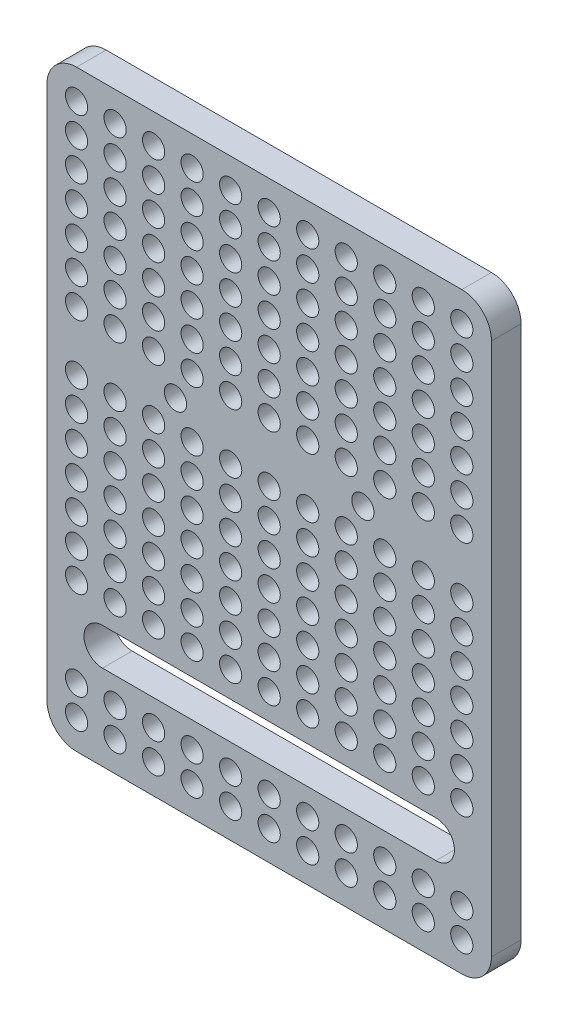
SolidWorks part; units mm, degrees
ref_plane "Спереди" through (0, 0, 0) normal (0, 0, 1) x (1, 0, 0)
ref_plane "Сверху" through (0, 0, 0) normal (0, 1, 0) x (1, 0, 0)
ref_plane "Справа" through (0, 0, 0) normal (1, 0, 0) x (0, 0, -1)
sketch "Эскиз1" plane through (0, 0, 0) normal (0, 0, 1) x (1, 0, 0)
  line L1 (4, 0) -> (56, 0)
  line L2 (0, 4) -> (0, 76)
  line L3 (4, 80) -> (56, 80)
  line L4 (60, 4) -> (60, 76)
  arc A0 (4, 0) -> (0, 4) centre (4, 4) cw
  arc A1 (56, 0) -> (60, 4) centre (56, 4) ccw
  arc A2 (56, 80) -> (60, 76) centre (56, 76) cw
  arc A3 (0, 76) -> (4, 80) centre (4, 76) cw
  point P7 (0, 0)
  point P12 (60, 80)
  point P15 (0, 80)
  dimension "D3" = 4
  dimension "D1" = 80
  dimension "D2" = 60
extrude "Бобышка-Вытянуть1" add sketch "Эскиз1" along normal blind 4 contours L3 A2 L4 A1 L1 A0 L2 A3
sketch "Эскиз2" plane through (0, 0, 4) normal (0, 0, 1) x (1, 0, 0)
  line L0 (30, 80) -> (30, 0) construction
  line L1 (4, 80) -> (56, 80) construction
  line L2 (4, 0) -> (56, 0) construction
  line L3 (7.5, 14) -> (52.5, 14) construction
  line L4 (7.5, 16.5) -> (52.5, 16.5)
  line L5 (7.5, 11.5) -> (52.5, 11.5)
  line L6 (0, 4) -> (0, 76) construction
  arc A0 (7.5, 16.5) -> (7.5, 11.5) centre (7.5, 14) ccw
  arc A1 (52.5, 11.5) -> (52.5, 16.5) centre (52.5, 14) ccw
  point P8 (30, 14)
  dimension "D1" = 11.5
  dimension "D2" = 7.5
extrude "Вырез-Вытянуть1" cut sketch "Эскиз2" against normal blind 4
sketch "Эскиз3" plane through (0, 0, 4) normal (0, 0, 1) x (1, 0, 0)
  line L0 (4, 80) -> (56, 80) construction
  line L1 (0, 4) -> (0, 76) construction
  line L2 (58.1, 64) -> (58.1, 60) construction
  line L4 (60, 4) -> (60, 76) construction
  circle A0 centre (4, 76) radius 1.5
  circle A1 centre (9.2, 76) radius 1.5
  circle A2 centre (14.4, 76) radius 1.5
  circle A3 centre (19.6, 76) radius 1.5
  circle A4 centre (24.8, 76) radius 1.5
  circle A5 centre (30, 76) radius 1.5
  circle A6 centre (35.2, 76) radius 1.5
  circle A7 centre (40.4, 76) radius 1.5
  circle A8 centre (45.6, 76) radius 1.5
  circle A9 centre (50.8, 76) radius 1.5
  circle A10 centre (56, 76) radius 1.5
  circle A11 centre (4, 72) radius 1.5
  circle A12 centre (9.2, 72) radius 1.5
  circle A13 centre (14.4, 72) radius 1.5
  circle A14 centre (19.6, 72) radius 1.5
  circle A15 centre (24.8, 72) radius 1.5
  circle A16 centre (30, 72) radius 1.5
  circle A17 centre (35.2, 72) radius 1.5
  circle A18 centre (40.4, 72) radius 1.5
  circle A19 centre (45.6, 72) radius 1.5
  circle A20 centre (50.8, 72) radius 1.5
  circle A21 centre (56, 72) radius 1.5
  circle A22 centre (4, 68) radius 1.5
  circle A23 centre (9.2, 68) radius 1.5
  circle A24 centre (14.4, 68) radius 1.5
  circle A25 centre (19.6, 68) radius 1.5
  circle A26 centre (24.8, 68) radius 1.5
  circle A27 centre (30, 68) radius 1.5
  circle A28 centre (35.2, 68) radius 1.5
  circle A29 centre (40.4, 68) radius 1.5
  circle A30 centre (45.6, 68) radius 1.5
  circle A31 centre (50.8, 68) radius 1.5
  circle A32 centre (56, 68) radius 1.5
  circle A33 centre (4, 64) radius 1.5
  circle A34 centre (9.2, 64) radius 1.5
  circle A35 centre (14.4, 64) radius 1.5
  circle A36 centre (19.6, 64) radius 1.5
  circle A37 centre (24.8, 64) radius 1.5
  circle A38 centre (30, 64) radius 1.5
  circle A39 centre (35.2, 64) radius 1.5
  circle A40 centre (40.4, 64) radius 1.5
  circle A41 centre (45.6, 64) radius 1.5
  circle A42 centre (50.8, 64) radius 1.5
  circle A43 centre (56, 64) radius 1.5
  circle A44 centre (4, 60) radius 1.5
  circle A45 centre (9.2, 60) radius 1.5
  circle A46 centre (14.4, 60) radius 1.5
  circle A47 centre (19.6, 60) radius 1.5
  circle A48 centre (24.8, 60) radius 1.5
  circle A49 centre (30, 60) radius 1.5
  circle A50 centre (35.2, 60) radius 1.5
  circle A51 centre (40.4, 60) radius 1.5
  circle A52 centre (45.6, 60) radius 1.5
  circle A53 centre (50.8, 60) radius 1.5
  circle A54 centre (56, 60) radius 1.5
  circle A55 centre (4, 56) radius 1.5
  circle A56 centre (9.2, 56) radius 1.5
  circle A57 centre (14.4, 56) radius 1.5
  circle A58 centre (19.6, 56) radius 1.5
  circle A59 centre (24.8, 56) radius 1.5
  circle A60 centre (30, 56) radius 1.5
  circle A61 centre (35.2, 56) radius 1.5
  circle A62 centre (40.4, 56) radius 1.5
  circle A63 centre (45.6, 56) radius 1.5
  circle A64 centre (50.8, 56) radius 1.5
  circle A65 centre (56, 56) radius 1.5
  circle A66 centre (4, 52) radius 1.5
  circle A67 centre (9.2, 52) radius 1.5
  circle A68 centre (14.4, 52) radius 1.5
  circle A69 centre (19.6, 52) radius 1.5
  circle A70 centre (24.8, 52) radius 1.5
  circle A71 centre (30, 52) radius 1.5
  circle A72 centre (35.2, 52) radius 1.5
  circle A73 centre (40.4, 52) radius 1.5
  circle A74 centre (45.6, 52) radius 1.5
  circle A75 centre (50.8, 52) radius 1.5
  circle A76 centre (56, 52) radius 1.5
  circle A88 centre (4, 44) radius 1.5
  circle A89 centre (9.2, 44) radius 1.5
  circle A90 centre (14.4, 44) radius 1.5
  circle A91 centre (19.6, 44) radius 1.5
  circle A92 centre (24.8, 44) radius 1.5
  circle A93 centre (30, 44) radius 1.5
  circle A94 centre (35.2, 44) radius 1.5
  circle A95 centre (40.4, 44) radius 1.5
  circle A96 centre (45.6, 44) radius 1.5
  circle A97 centre (50.8, 44) radius 1.5
  circle A98 centre (56, 44) radius 1.5
  circle A99 centre (4, 40) radius 1.5
  circle A100 centre (9.2, 40) radius 1.5
  circle A101 centre (14.4, 40) radius 1.5
  circle A102 centre (19.6, 40) radius 1.5
  circle A103 centre (24.8, 40) radius 1.5
  circle A104 centre (30, 40) radius 1.5
  circle A105 centre (35.2, 40) radius 1.5
  circle A106 centre (40.4, 40) radius 1.5
  circle A107 centre (45.6, 40) radius 1.5
  circle A108 centre (50.8, 40) radius 1.5
  circle A109 centre (56, 40) radius 1.5
  circle A110 centre (4, 36) radius 1.5
  circle A111 centre (9.2, 36) radius 1.5
  circle A112 centre (14.4, 36) radius 1.5
  circle A113 centre (19.6, 36) radius 1.5
  circle A114 centre (24.8, 36) radius 1.5
  circle A115 centre (30, 36) radius 1.5
  circle A116 centre (35.2, 36) radius 1.5
  circle A117 centre (40.4, 36) radius 1.5
  circle A118 centre (45.6, 36) radius 1.5
  circle A119 centre (50.8, 36) radius 1.5
  circle A120 centre (56, 36) radius 1.5
  circle A121 centre (4, 32) radius 1.5
  circle A122 centre (9.2, 32) radius 1.5
  circle A123 centre (14.4, 32) radius 1.5
  circle A124 centre (19.6, 32) radius 1.5
  circle A125 centre (24.8, 32) radius 1.5
  circle A126 centre (30, 32) radius 1.5
  circle A127 centre (35.2, 32) radius 1.5
  circle A128 centre (40.4, 32) radius 1.5
  circle A129 centre (45.6, 32) radius 1.5
  circle A130 centre (50.8, 32) radius 1.5
  circle A131 centre (56, 32) radius 1.5
  circle A132 centre (4, 28) radius 1.5
  circle A133 centre (9.2, 28) radius 1.5
  circle A134 centre (14.4, 28) radius 1.5
  circle A135 centre (19.6, 28) radius 1.5
  circle A136 centre (24.8, 28) radius 1.5
  circle A137 centre (30, 28) radius 1.5
  circle A138 centre (35.2, 28) radius 1.5
  circle A139 centre (40.4, 28) radius 1.5
  circle A140 centre (45.6, 28) radius 1.5
  circle A141 centre (50.8, 28) radius 1.5
  circle A142 centre (56, 28) radius 1.5
  circle A143 centre (4, 24) radius 1.5
  circle A144 centre (9.2, 24) radius 1.5
  circle A145 centre (14.4, 24) radius 1.5
  circle A146 centre (19.6, 24) radius 1.5
  circle A147 centre (24.8, 24) radius 1.5
  circle A148 centre (30, 24) radius 1.5
  circle A149 centre (35.2, 24) radius 1.5
  circle A150 centre (40.4, 24) radius 1.5
  circle A151 centre (45.6, 24) radius 1.5
  circle A152 centre (50.8, 24) radius 1.5
  circle A153 centre (56, 24) radius 1.5
  circle A154 centre (4, 20) radius 1.5
  circle A155 centre (9.2, 20) radius 1.5
  circle A156 centre (14.4, 20) radius 1.5
  circle A157 centre (19.6, 20) radius 1.5
  circle A158 centre (24.8, 20) radius 1.5
  circle A159 centre (30, 20) radius 1.5
  circle A160 centre (35.2, 20) radius 1.5
  circle A161 centre (40.4, 20) radius 1.5
  circle A162 centre (45.6, 20) radius 1.5
  circle A163 centre (50.8, 20) radius 1.5
  circle A164 centre (56, 20) radius 1.5
  circle A187 centre (4, 8) radius 1.5
  circle A188 centre (9.2, 8) radius 1.5
  circle A189 centre (14.4, 8) radius 1.5
  circle A190 centre (19.6, 8) radius 1.5
  circle A191 centre (24.8, 8) radius 1.5
  circle A192 centre (30, 8) radius 1.5
  circle A193 centre (35.2, 8) radius 1.5
  circle A194 centre (40.4, 8) radius 1.5
  circle A195 centre (45.6, 8) radius 1.5
  circle A196 centre (50.8, 8) radius 1.5
  circle A197 centre (56, 8) radius 1.5
  circle A198 centre (4, 4) radius 1.5
  circle A199 centre (9.2, 4) radius 1.5
  circle A200 centre (14.4, 4) radius 1.5
  circle A201 centre (19.6, 4) radius 1.5
  circle A202 centre (24.8, 4) radius 1.5
  circle A203 centre (30, 4) radius 1.5
  circle A204 centre (35.2, 4) radius 1.5
  circle A205 centre (40.4, 4) radius 1.5
  circle A206 centre (45.6, 4) radius 1.5
  circle A207 centre (50.8, 4) radius 1.5
  circle A208 centre (56, 4) radius 1.5
  circle A209 centre (9.2, 16) radius 1.5 [skipped]
  circle A210 centre (14.4, 16) radius 1.5 [skipped]
  circle A211 centre (19.6, 16) radius 1.5 [skipped]
  circle A212 centre (24.8, 16) radius 1.5 [skipped]
  circle A213 centre (30, 16) radius 1.5 [skipped]
  circle A214 centre (35.2, 16) radius 1.5 [skipped]
  circle A215 centre (40.4, 16) radius 1.5 [skipped]
  circle A216 centre (45.6, 16) radius 1.5 [skipped]
  circle A217 centre (50.8, 16) radius 1.5 [skipped]
  circle A218 centre (50.8, 12) radius 1.5 [skipped]
  circle A219 centre (45.6, 12) radius 1.5 [skipped]
  circle A220 centre (40.4, 12) radius 1.5 [skipped]
  circle A221 centre (35.2, 12) radius 1.5 [skipped]
  circle A222 centre (30, 12) radius 1.5 [skipped]
  circle A223 centre (24.8, 12) radius 1.5 [skipped]
  circle A224 centre (19.6, 12) radius 1.5 [skipped]
  circle A225 centre (14.4, 12) radius 1.5 [skipped]
  circle A226 centre (9.2, 12) radius 1.5 [skipped]
  circle A227 centre (4, 12) radius 1.5 [skipped]
  circle A228 centre (4, 16) radius 1.5 [skipped]
  circle A229 centre (56, 16) radius 1.5 [skipped]
  circle A230 centre (56, 12) radius 1.5 [skipped]
  circle A265 centre (4, 48) radius 1.5 [skipped]
  circle A266 centre (9.2, 48) radius 1.5 [skipped]
  circle A267 centre (14.4, 48) radius 1.5 [skipped]
  circle A268 centre (19.6, 48) radius 1.5 [skipped]
  circle A269 centre (24.8, 48) radius 1.5 [skipped]
  circle A270 centre (30, 48) radius 1.5 [skipped]
  circle A271 centre (35.2, 48) radius 1.5 [skipped]
  circle A272 centre (40.4, 48) radius 1.5 [skipped]
  circle A273 centre (45.6, 48) radius 1.5 [skipped]
  circle A274 centre (50.8, 48) radius 1.5 [skipped]
  circle A275 centre (56, 48) radius 1.5 [skipped]
  circle A276 centre (17.35, 47.9985) radius 1.5
  circle A277 centre (42.65, 47.9985) radius 1.5
  dimension "D1" = 3
  dimension "D2" = 4
  dimension "D3" = 4
  dimension "D7" = 5.2
  dimension "D8" = 4
  dimension "D9" = 3
  dimension "D6" = 4
  dimension "D10" = 17.35
  dimension "D11" = 3
  dimension "D12" = 25.3
  dimension "D13" = 17.35
  dimension "D4" = 11
  dimension "D5" = 19
extrude "Вырез-Вытянуть2" cut sketch "Эскиз3" against normal blind 4
